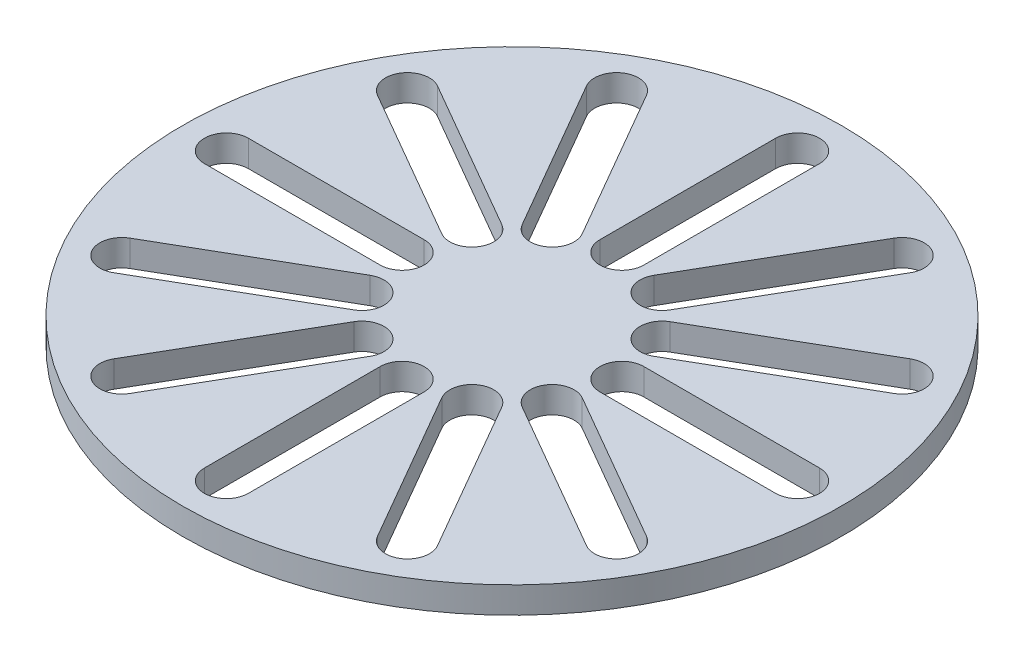
SolidWorks part; units mm, degrees
ref_plane "Front Plane" through (0, 0, 0) normal (0, 0, 1) x (1, 0, 0)
ref_plane "Top Plane" through (0, 0, 0) normal (0, 1, 0) x (1, 0, 0)
ref_plane "Right Plane" through (0, 0, 0) normal (1, 0, 0) x (0, 0, -1)
sketch "Sketch1" plane through (0, 0, 0) normal (0, 1, 0) x (1, 0, 0)
  line L2 (6.35, 82.55) -> (6.35, 31.75)
  line L3 (35.7757, 74.6654) -> (10.3757, 30.6713)
  line L4 (46.7743, 68.3154) -> (21.3743, 24.3213)
  line L6 (68.3154, 46.7743) -> (24.3213, 21.3743)
  line L8 (-6.35, 82.55) -> (-6.35, 31.75)
  line L10 (74.6654, 35.7757) -> (30.6713, 10.3757)
  line L11 (82.55, 6.35) -> (31.75, 6.35)
  line L12 (82.55, -6.35) -> (31.75, -6.35)
  line L13 (74.6654, -35.7757) -> (30.6713, -10.3757)
  line L14 (68.3154, -46.7743) -> (24.3213, -21.3743)
  line L15 (46.7743, -68.3154) -> (21.3743, -24.3213)
  line L16 (35.7757, -74.6654) -> (10.3757, -30.6713)
  line L17 (6.35, -82.55) -> (6.35, -31.75)
  line L18 (-6.35, -82.55) -> (-6.35, -31.75)
  line L19 (-35.7757, -74.6654) -> (-10.3757, -30.6713)
  line L20 (-46.7743, -68.3154) -> (-21.3743, -24.3213)
  line L21 (-68.3154, -46.7743) -> (-24.3213, -21.3743)
  line L22 (-74.6654, -35.7757) -> (-30.6713, -10.3757)
  line L23 (-82.55, -6.35) -> (-31.75, -6.35)
  line L24 (-82.55, 6.35) -> (-31.75, 6.35)
  line L25 (-74.6654, 35.7757) -> (-30.6713, 10.3757)
  line L26 (-68.3154, 46.7743) -> (-24.3213, 21.3743)
  line L27 (-46.7743, 68.3154) -> (-21.3743, 24.3213)
  line L28 (-35.7757, 74.6654) -> (-10.3757, 30.6713)
  circle A0 centre (0, 0) radius 95.25
  arc A3 (6.35, 82.55) -> (-6.35, 82.55) centre (0, 82.55) ccw
  arc A4 (-6.35, 31.75) -> (6.35, 31.75) centre (0, 31.75) ccw
  arc A5 (10.3757, 30.6713) -> (21.3743, 24.3213) centre (15.875, 27.4963) ccw
  arc A6 (46.7743, 68.3154) -> (35.7757, 74.6654) centre (41.275, 71.4904) ccw
  arc A7 (24.3213, 21.3743) -> (30.6713, 10.3757) centre (27.4963, 15.875) ccw
  arc A8 (74.6654, 35.7757) -> (68.3154, 46.7743) centre (71.4904, 41.275) ccw
  arc A9 (31.75, 6.35) -> (31.75, -6.35) centre (31.75, 0) ccw
  arc A10 (82.55, -6.35) -> (82.55, 6.35) centre (82.55, 0) ccw
  arc A11 (30.6713, -10.3757) -> (24.3213, -21.3743) centre (27.4963, -15.875) ccw
  arc A12 (68.3154, -46.7743) -> (74.6654, -35.7757) centre (71.4904, -41.275) ccw
  arc A13 (21.3743, -24.3213) -> (10.3757, -30.6713) centre (15.875, -27.4963) ccw
  arc A14 (35.7757, -74.6654) -> (46.7743, -68.3154) centre (41.275, -71.4904) ccw
  arc A15 (6.35, -31.75) -> (-6.35, -31.75) centre (0, -31.75) ccw
  arc A16 (-6.35, -82.55) -> (6.35, -82.55) centre (0, -82.55) ccw
  arc A17 (-10.3757, -30.6713) -> (-21.3743, -24.3213) centre (-15.875, -27.4963) ccw
  arc A18 (-46.7743, -68.3154) -> (-35.7757, -74.6654) centre (-41.275, -71.4904) ccw
  arc A19 (-24.3213, -21.3743) -> (-30.6713, -10.3757) centre (-27.4963, -15.875) ccw
  arc A20 (-74.6654, -35.7757) -> (-68.3154, -46.7743) centre (-71.4904, -41.275) ccw
  arc A21 (-31.75, -6.35) -> (-31.75, 6.35) centre (-31.75, 0) ccw
  arc A22 (-82.55, 6.35) -> (-82.55, -6.35) centre (-82.55, 0) ccw
  arc A23 (-30.6713, 10.3757) -> (-24.3213, 21.3743) centre (-27.4963, 15.875) ccw
  arc A24 (-68.3154, 46.7743) -> (-74.6654, 35.7757) centre (-71.4904, 41.275) ccw
  arc A25 (-21.3743, 24.3213) -> (-10.3757, 30.6713) centre (-15.875, 27.4963) ccw
  arc A26 (-35.7757, 74.6654) -> (-46.7743, 68.3154) centre (-41.275, 71.4904) ccw
  point P78 (0, 0)
  dimension "D1" = 190.5
  dimension "D3" = 31.75
  dimension "D4" = 6.35
  dimension "D2" = 50.8
  dimension "D5" = 12.7
  dimension "D7" = 0
  dimension "D8" = 0
  dimension "D9" = 12
extrude "Boss-Extrude3" add sketch "Sketch1" along normal blind 7.62
scale "Scale1" scale about centroid uniform scaling yes scale factor 2
